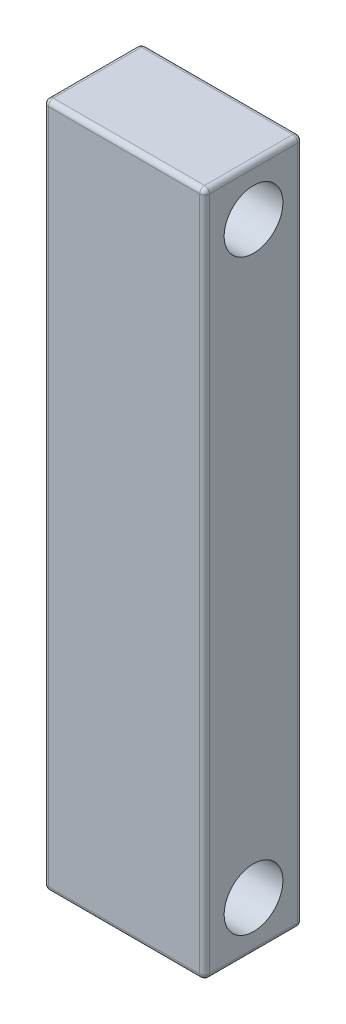
SolidWorks part; units mm, degrees
material "AISI 1020 Steel, Cold Rolled"
ref_plane "Front Plane" through (0, 0, 0) normal (0, 0, 1) x (1, 0, 0)
ref_plane "Top Plane" through (0, 0, 0) normal (0, 1, 0) x (1, 0, 0)
ref_plane "Right Plane" through (0, 0, 0) normal (1, 0, 0) x (0, 0, -1)
sketch "Sketch1" plane through (0, 0, 0) normal (0, 0, 1) x (1, 0, 0)
  line L1 (-16.45, 70) -> (16.45, 70)
  line L2 (-16.45, 70) -> (-16.45, -70)
  line L3 (-16.45, -70) -> (16.45, -70)
  line L4 (16.45, 70) -> (16.45, -70)
  line L5 (-16.45, 70) -> (16.45, -70) construction
  line L6 (-16.45, -70) -> (16.45, 70) construction
  point P0 (0, 0)
  dimension "D1" = 140
  dimension "D2" = 32.9
extrude "Boss-Extrude1" add sketch "Sketch1" along normal blind 20
sketch "Sketch3" plane through (16.45, 0, 0) normal (1, 0, 0) x (0, 0, -1)
  circle A0 centre (-10, 60) radius 6
  circle A1 centre (-10, -60) radius 6
extrude "Cut-Extrude1" cut sketch "Sketch3" against normal through all
fillet "Fillet1" radius 1 12 edges at (-16.45, 0, 0) (-16.45, -70, 10) (0, -70, 0) (0, -70, 20) (16.45, -70, 10) (-16.45, 0, 20) (-16.45, 70, 10) (0, 70, 0) (16.45, 0, 0) (16.45, 0, 20) (0, 70, 20) (16.45, 70, 10)
